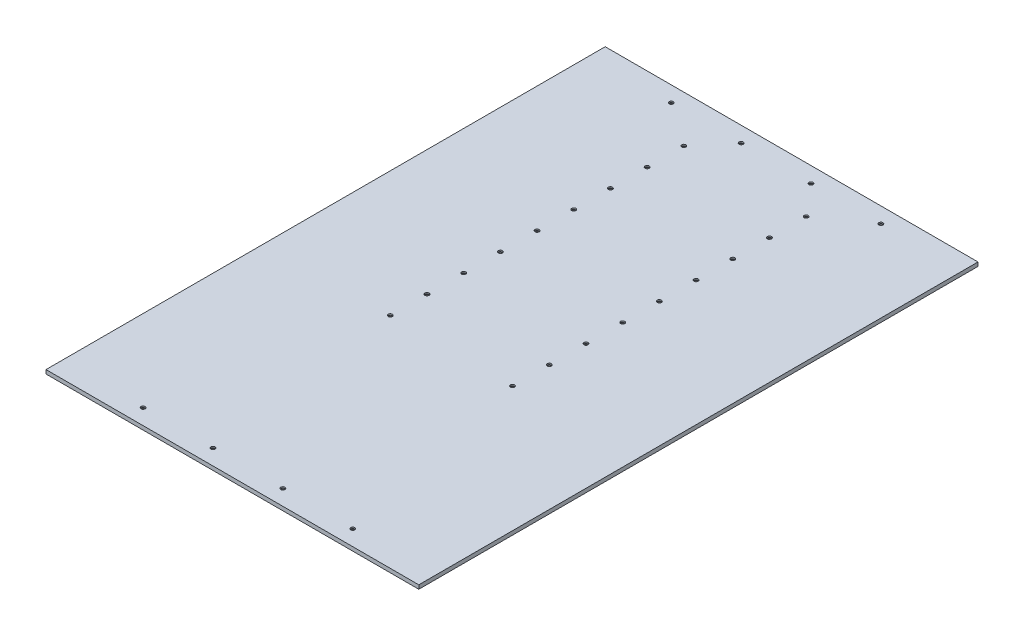
SolidWorks part; units mm, degrees
material "6061 Alloy"
ref_plane "Front Plane" through (0, 0, 0) normal (0, 0, 1) x (1, 0, 0)
ref_plane "Top Plane" through (0, 0, 0) normal (0, 1, 0) x (1, 0, 0)
ref_plane "Right Plane" through (0, 0, 0) normal (1, 0, 0) x (0, 0, -1)
sketch "Sketch1" plane through (0, 0, 0) normal (0, 1, 0) x (1, 0, 0)
  line L1 (304.8, -457.2) -> (-304.8, -457.2)
  line L2 (304.8, -457.2) -> (304.8, 457.2)
  line L3 (304.8, 457.2) -> (-304.8, 457.2)
  line L4 (-304.8, -457.2) -> (-304.8, 457.2)
  line L5 (304.8, -457.2) -> (-304.8, 457.2) construction
  line L6 (304.8, 457.2) -> (-304.8, -457.2) construction
  point P0 (0, 0)
  dimension "D1" = 914.4
  dimension "D2" = 609.6
extrude "Boss-Extrude1" add sketch "Sketch1" along normal blind 6.35 separate body
sketch "Sketch2" plane through (0, 0, 0) normal (0, -1, 0) x (1, 0, 0)
  point P0 (-171.45, 431.8)
hole_wizard "CBORE for 1/4 Binding Head Machine Screw1" positions "Sketch2" profile "Sketch3" counterbore size "1/4" standard "ANSI Inch" end condition through all
sketch "Sketch3" plane through (-171.45, 0, 431.8) normal (1, 0, 0) x (0, 0, -1)
  line L0 (0, 0) -> (0, 6.35)
  line L1 (0, 6.35) -> (3.3782, 6.35)
  line L3 (3.3782, 6.35) -> (3.3782, 4.191)
  line L4 (3.3782, 4.191) -> (7.1437, 4.191)
  line L5 (7.1437, 4.191) -> (7.1437, 0)
  line L7 (7.1437, 0) -> (0, 0)
  line L11 (0, -6.35) -> (0, 107.95) construction
  dimension "Thru Hole Dia." = 6.7564
  dimension "Thru Hole Depth" = 6.35
  dimension "C'Bore Dia." = 14.2875
  dimension "C'Bore Depth" = 4.191
pattern_linear "LPattern1" count 4 spacing 114.3 along (1, 0, 0) of "CBORE for 1/4 Binding Head Machine Screw1"
sketch "Sketch4" plane through (0, 0, 0) normal (0, -1, 0) x (1, 0, 0)
  point P0 (171.45, -431.8)
hole_wizard "CBORE for 1/4 Binding Head Machine Screw2" positions "Sketch4" profile "Sketch5" counterbore size "1/4" standard "ANSI Inch" end condition through all
sketch "Sketch5" plane through (171.45, 0, -431.8) normal (1, 0, 0) x (0, 0, -1)
  line L0 (0, 0) -> (0, 6.35)
  line L1 (0, 6.35) -> (3.3782, 6.35)
  line L3 (3.3782, 6.35) -> (3.3782, 4.191)
  line L4 (3.3782, 4.191) -> (7.1437, 4.191)
  line L5 (7.1437, 4.191) -> (7.1437, 0)
  line L7 (7.1437, 0) -> (0, 0)
  line L11 (0, -6.35) -> (0, 107.95) construction
  dimension "Thru Hole Dia." = 6.7564
  dimension "Thru Hole Depth" = 6.35
  dimension "C'Bore Dia." = 14.2875
  dimension "C'Bore Depth" = 4.191
pattern_linear "LPattern2" count 4 spacing 114.3 along (-1, 0, 0) of "CBORE for 1/4 Binding Head Machine Screw2"
sketch "Sketch6" plane through (0, 0, 0) normal (0, -1, 0) x (1, 0, 0)
  line L0 (304.8, -457.2) -> (-304.8, -457.2) construction
  line L1 (-311.15, -457.2) -> (-311.15, 457.2) construction
  point P0 (-100, -381)
  dimension "D1" = 76.2
  dimension "D2" = 211.15
hole_wizard "CBORE for 1/4 Binding Head Machine Screw4" positions "Sketch6" profile "Sketch7" counterbore size "1/4" standard "ANSI Inch" end condition through all
sketch "Sketch7" plane through (-100, 0, -381) normal (1, 0, 0) x (0, 0, -1)
  line L0 (0, 0) -> (0, 6.35)
  line L1 (0, 6.35) -> (3.3782, 6.35)
  line L3 (3.3782, 6.35) -> (3.3782, 4.191)
  line L4 (3.3782, 4.191) -> (7.1437, 4.191)
  line L5 (7.1437, 4.191) -> (7.1437, 0)
  line L7 (7.1437, 0) -> (0, 0)
  line L11 (0, -6.35) -> (0, 107.95) construction
  dimension "Thru Hole Dia." = 6.7564
  dimension "Thru Hole Depth" = 6.35
  dimension "C'Bore Dia." = 14.2875
  dimension "C'Bore Depth" = 4.191
pattern_linear "LPattern3" count 2 spacing 200 along (1, 0, 0) count 9 spacing 60 along (0, 0, 1) of "CBORE for 1/4 Binding Head Machine Screw4"
